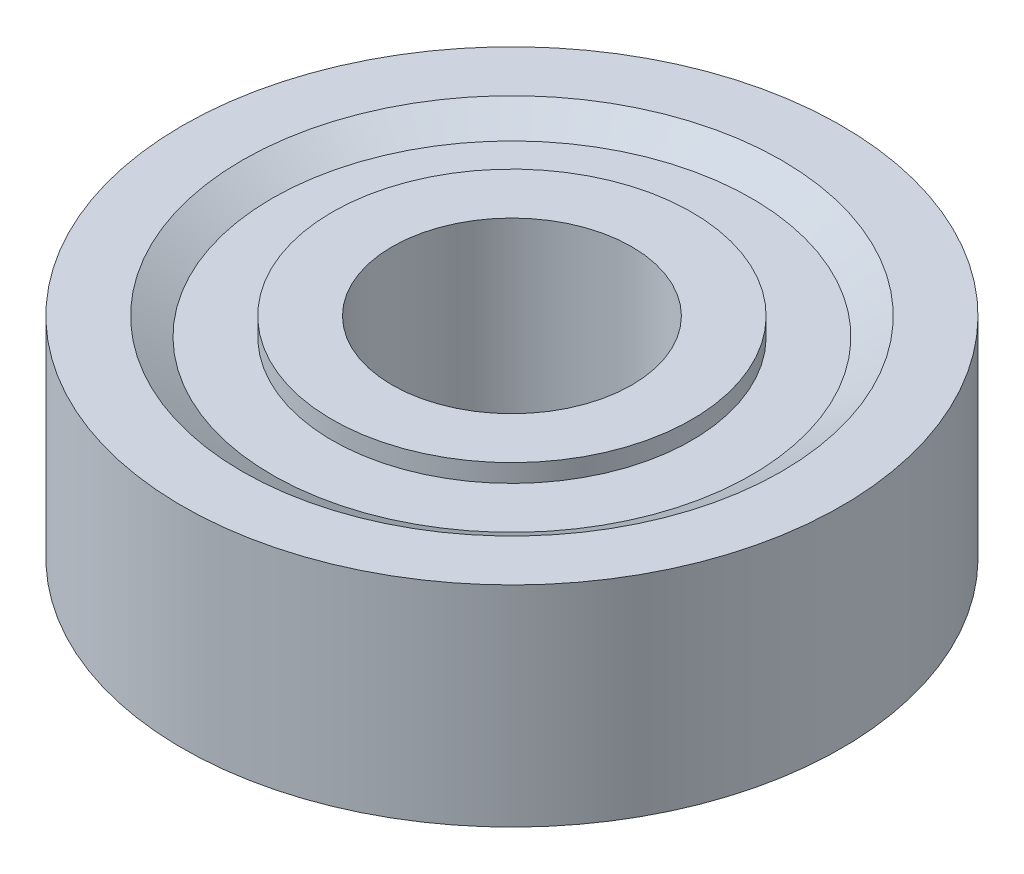
SolidWorks part; units mm, degrees
ref_plane "Ön Düzlem" through (0, 0, 0) normal (0, 0, 1) x (1, 0, 0)
ref_plane "Üst Düzlem" through (0, 0, 0) normal (0, 1, 0) x (1, 0, 0)
ref_plane "Sağ Düzlem" through (0, 0, 0) normal (1, 0, 0) x (0, 0, -1)
sketch "Çizim1" plane through (0, 0, 0) normal (0, 0, 1) x (1, 0, 0)
  line L2 (-3.72, 0) -> (-4.72, -0.6)
  line L3 (-4.72, -0.6) -> (-6.72, -0.6)
  line L4 (-6.72, -0.6) -> (-6.72, 6.4)
  line L5 (-6.72, 6.4) -> (-4.72, 6.4)
  line L6 (-4.72, 6.4) -> (-3.72, 5.8)
  line L7 (-3.72, 5.8) -> (-1.72, 5.8)
  line L8 (-1.72, 5.8) -> (-1.72, 6.4)
  line L9 (-1.72, 6.4) -> (0.28, 6.4)
  line L11 (-3.72, 0) -> (-1.72, 0)
  line L12 (-1.72, 0) -> (-1.72, -0.6)
  line L13 (-1.72, -0.6) -> (0.28, -0.6)
  line L16 (4.28, 8.1627) -> (4.28, -2.5513) construction
  line L17 (0.28, 6.4) -> (0.28, -0.6)
  dimension "D2" = 7
  dimension "D3" = 2
  dimension "D4" = 2
  dimension "D5" = 2
  dimension "D6" = 2
  dimension "D7" = 7
  dimension "D8" = 5.8
  dimension "D9" = 0.6
  dimension "D10" = 2
  dimension "D11" = 2
  dimension "D12" = 11
revolve "Döndür1" add sketch "Çizim1" angle 360 about L16
